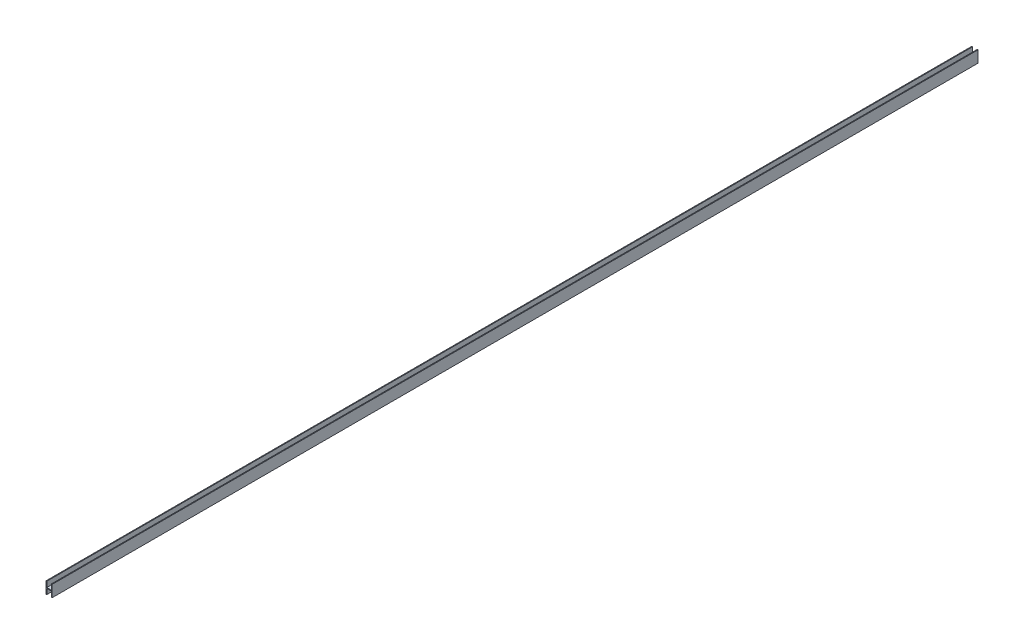
SolidWorks part; units mm, degrees
material "6063-T5"
ref_plane "前视基准面" through (0, 0, 0) normal (0, 0, 1) x (1, 0, 0)
ref_plane "上视基准面" through (0, 0, 0) normal (0, 1, 0) x (1, 0, 0)
ref_plane "右视基准面" through (0, 0, 0) normal (1, 0, 0) x (0, 0, -1)
sketch "草图1" plane through (0, 0, 0) normal (0, 0, 1) x (1, 0, 0)
  line L1 (-4, -7.5) -> (4, -7.5)
  line L2 (-4, -7.5) -> (-4, 7.5)
  line L3 (-4, 7.5) -> (4, 7.5)
  line L4 (4, -7.5) -> (4, 7.5)
  line L5 (-4, -7.5) -> (4, 7.5) construction
  line L6 (-4, 7.5) -> (4, -7.5) construction
  point P0 (0, 0)
  dimension "D1" = 15
  dimension "D2" = 8
extrude "凸台-拉伸1" add sketch "草图1" along normal blind 1200
sketch "草图2" plane through (0, 0, 0) normal (0, 0, -1) x (-1, 0, 0)
  line L0 (4, -7.5) -> (-4, -7.5) construction
  line L1 (-3, -14.5) -> (3, -14.5)
  line L2 (-3, -14.5) -> (-3, -0.5)
  line L3 (-3, -0.5) -> (3, -0.5)
  line L4 (3, -14.5) -> (3, -0.5)
  line L5 (-3, -14.5) -> (3, -0.5) construction
  line L6 (-3, -0.5) -> (3, -14.5) construction
  line L7 (-4, 7.5) -> (4, 7.5) construction
  line L8 (-3, 0.5) -> (3, 0.5)
  line L9 (-3, 0.5) -> (-3, 14.5)
  line L10 (-3, 14.5) -> (3, 14.5)
  line L11 (3, 0.5) -> (3, 14.5)
  line L12 (-3, 0.5) -> (3, 14.5) construction
  line L13 (-3, 14.5) -> (3, 0.5) construction
  point P0 (0, -7.5)
  point P7 (0, 7.5)
  dimension "D1" = 6
  dimension "D2" = 6
  dimension "D3" = 0.5
  dimension "D4" = 0.5
extrude "切除-拉伸1" cut sketch "草图2" against normal blind 2400
